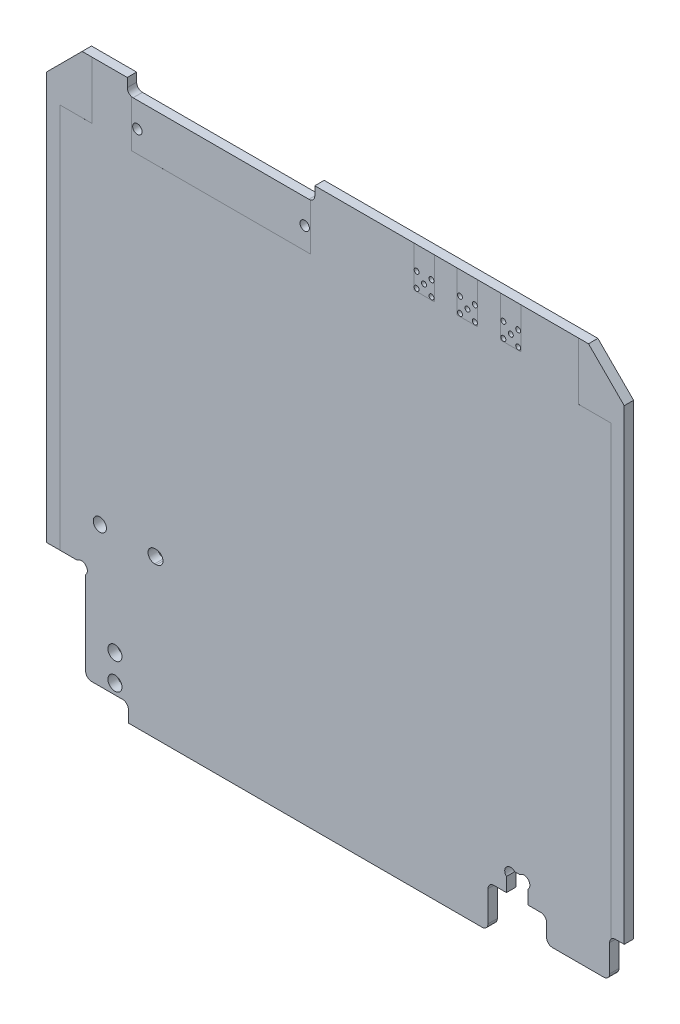
SolidWorks part; units mm, degrees
material "FR4_stuffedProtoboard"
ref_plane "Front Plane" through (0, 0, 0) normal (0, 0, 1) x (1, 0, 0)
ref_plane "Top Plane" through (0, 0, 0) normal (0, 1, 0) x (1, 0, 0)
ref_plane "Right Plane" through (0, 0, 0) normal (1, 0, 0) x (0, 0, -1)
ref_plane "Plane4" through (0, 0, -0.0125) normal (0, 0, -1) x (-1, 0, 0)
sketch "Sketch1" plane through (0, 0, -0.0125) normal (0, 0, -1) x (-1, 0, 0)
  line L0 (35.3, -50) -> (35.3, -48)
  line L1 (36.3, -47) -> (45.8, -47)
  line L2 (46.8, -46) -> (46.8, -41.4)
  line L3 (47.8, -40.4) -> (49.3, -40.4)
  line L4 (49.3, -40.4) -> (49.3, 39.2)
  line L5 (49.3, 39.2) -> (43.2, 45.3)
  line L6 (43.2, 45.3) -> (35.5, 45.3)
  line L7 (35.5, 45.3) -> (35.5, 43.8)
  line L8 (34.5, 42.8) -> (4.5, 42.8)
  line L9 (3.5, 43.8) -> (3.5, 45.3)
  line L10 (3.5, 45.3) -> (-43.2, 45.3)
  line L11 (-43.2, 45.3) -> (-49.3, 39.2)
  line L12 (-49.3, 39.2) -> (-49.3, -40.4)
  line L13 (-49.3, -40.4) -> (-47.8, -40.4)
  line L14 (-46.8, -41.4) -> (-46.8, -46)
  line L15 (-45.8, -47) -> (-36.3, -47)
  line L16 (-35.3, -48) -> (-35.3, -50)
  line L17 (-35.3, -50) -> (35.3, -50)
  line L18 (0, -50) -> (0, 45.3) construction
  line L19 (19.5, 42.8) -> (19.5, 25.5258) construction
  line L20 (-13.87, 41.37) -> (-16.41, 38.83) construction
  line L21 (-21.27, 41.37) -> (-23.81, 38.83) construction
  line L22 (-28.67, 41.37) -> (-31.21, 38.83) construction
  arc A0 (35.3, -48) -> (36.3, -47) centre (36.3, -48) cw
  arc A1 (45.8, -47) -> (46.8, -46) centre (45.8, -46) ccw
  arc A2 (46.8, -41.4) -> (47.8, -40.4) centre (47.8, -41.4) cw
  arc A3 (35.5, 43.8) -> (34.5, 42.8) centre (34.5, 43.8) cw
  arc A4 (4.5, 42.8) -> (3.5, 43.8) centre (4.5, 43.8) cw
  arc A5 (-47.8, -40.4) -> (-46.8, -41.4) centre (-47.8, -41.4) cw
  arc A6 (-46.8, -46) -> (-45.8, -47) centre (-45.8, -46) ccw
  arc A7 (-36.3, -47) -> (-35.3, -48) centre (-36.3, -48) cw
  circle A8 centre (-21.27, 41.37) radius 0.425
  circle A9 centre (-23.81, 41.37) radius 0.425
  circle A10 centre (-22.54, 40.1) radius 0.425
  circle A11 centre (-13.87, 41.37) radius 0.425
  circle A12 centre (-23.81, 38.83) radius 0.425
  circle A13 centre (-16.41, 41.37) radius 0.425
  circle A14 centre (-15.14, 40.1) radius 0.425
  circle A15 centre (-21.27, 38.83) radius 0.425
  circle A16 centre (-28.67, 41.37) radius 0.425
  circle A17 centre (-31.21, 41.37) radius 0.425
  circle A18 centre (-16.41, 38.83) radius 0.425
  circle A19 centre (-29.94, 40.1) radius 0.425
  circle A20 centre (-31.21, 38.83) radius 0.425
  circle A21 centre (-28.67, 38.83) radius 0.425
  circle A22 centre (33.775, 38.54) radius 0.8
  circle A23 centre (5.225, 38.54) radius 0.8
  circle A24 centre (-13.87, 38.83) radius 0.425
  point P35 (-15.14, 40.1)
  dimension "D7" = 2.5
  dimension "D8" = 1.6
  dimension "D9" = 14.275
  dimension "D10" = 4.26
  dimension "D11" = 1
  dimension "D12" = 1
  dimension "D13" = 1
  dimension "D14" = 1
  dimension "D15" = 1
  dimension "D16" = 1
  dimension "D17" = 1
  dimension "D18" = 1
  dimension "D26" = 0.85
  dimension "D1" = 98.6
  dimension "D2" = 95.3
  dimension "D3" = 14
  dimension "D4" = 9.6
  dimension "D5" = 2.5
  dimension "D6" = 3
  dimension "D19" = 14
  dimension "D20" = 2.5
  dimension "D21" = 6.1
  dimension "D22" = 6.1
  dimension "D23" = 32
  dimension "D24" = 2.54
  dimension "D25" = 2.54
  dimension "D28" = 7.4
  dimension "D29" = 3.93
  dimension "D30" = 35.43
  dimension "D31" = 45
  dimension "D32" = 45
  dimension "D33" = 29.8
  dimension "D34" = 50
  dimension "D27" = 3
extrude "Boss-Extrude1" add sketch "Sketch1" against normal blind 1.6
sketch "thermalContacts_lower" plane through (0, 0, -0.0125) normal (0, 0, -1) x (-1, 0, 0)
  line L3 (47, 35.5) -> (47, -41.5)
  line L4 (41.5, 35.5) -> (41.5, 41.5)
  line L5 (41.5, 35.5) -> (47, 35.5)
  line L9 (-47, 35.5) -> (-47, -41.5)
  line L10 (-41.5, 35.5) -> (-47, 35.5)
  line L11 (-41.5, 35.5) -> (-41.5, 41.5)
  line L14 (-41.5, 41.5) -> (-41.5, 47)
  line L15 (-41.5, 41.5) -> (-49.5, 41.5) construction
  line L18 (41.5, 41.5) -> (41.5, 48.7577)
  line L19 (41.5, 41.5) -> (49.5, 41.5) construction
  line L20 (47, -41.5) -> (59.8273, -41.5)
  line L21 (59.8273, -41.5) -> (59.8273, 48.7577)
  line L22 (-56.1922, 47) -> (-41.5, 47)
  line L23 (41.5, 48.7577) -> (59.8273, 48.7577)
  line L24 (-56.1922, 47) -> (-56.1922, -41.5)
  line L25 (-47, -41.5) -> (-56.1922, -41.5)
  line L26 (43.2, 45.3) -> (35.5, 45.3) construction
  line L27 (49.3, -40.4) -> (49.3, 39.2) construction
  line L28 (-35.3, -50) -> (35.3, -50) construction
  line L29 (-49.3, 39.2) -> (-49.3, -40.4) construction
  line L30 (3.5, 45.3) -> (-43.2, 45.3) construction
  dimension "D1" = 9.8
  dimension "D2" = 7.8
  dimension "D3" = 2.3
  dimension "D4" = 8.5
  dimension "D5" = 8.5
  dimension "D6" = 2.3
  dimension "D7" = 7.8
  dimension "D8" = 9.8
sketch "thermalContacts_upper" plane through (0, 0, 1.5875) normal (0, 0, 1) x (1, 0, 0)
  line L3 (-47, 35.5) -> (-47, -41.5)
  line L4 (-41.5, 35.5) -> (-41.5, 41.5)
  line L5 (-41.5, 35.5) -> (-47, 35.5)
  line L9 (47, 35.5) -> (47, -41.5)
  line L10 (41.5, 35.5) -> (47, 35.5)
  line L11 (41.5, 35.5) -> (41.5, 41.5)
  line L14 (41.5, 41.5) -> (41.5, 47)
  line L15 (41.5, 41.5) -> (49.5, 41.5) construction
  line L18 (-41.5, 41.5) -> (-41.5, 47)
  line L19 (-41.5, 41.5) -> (-49.5, 41.5) construction
  line L20 (47, -41.5) -> (59.8273, -41.5)
  line L21 (59.8273, -41.5) -> (59.8273, 47)
  line L22 (59.8273, 47) -> (41.5, 47)
  line L23 (-41.5, 47) -> (-56.1922, 47)
  line L24 (-56.1922, 47) -> (-56.1922, -41.5)
  line L25 (-56.1922, -41.5) -> (-47, -41.5)
extrude "Cut-Extrude1" cut sketch "thermalContacts_lower" against normal blind 0.0001
extrude "Cut-Extrude2" cut sketch "thermalContacts_upper" against normal blind 0.0001
sketch "partFootprints" plane through (0, 0, 1.5875) normal (0, 0, 1) x (1, 0, 0)
  line L0 (-34.74, 34.84) -> (-34.74, 42.8292)
  line L1 (-4.26, 34.84) -> (-34.74, 34.84)
  line L2 (-41.5, 45.3) -> (-35.5, 45.3) construction
  line L3 (-36.1132, 45.3) -> (-39.5054, 45.3) construction
  line L4 (-4.26, 34.84) -> (-4.26, 42.8292)
  line L5 (-49.3, -40.4) -> (-49.3, 39.2) construction
  line L6 (13.39, 45.3) -> (13.39, 38.35)
  line L7 (13.39, 38.35) -> (16.89, 38.35)
  line L8 (16.89, 38.35) -> (16.89, 45.3)
  line L9 (16.89, 45.3) -> (13.39, 45.3)
  line L10 (20.79, 45.3) -> (20.79, 38.35)
  line L11 (20.79, 38.35) -> (24.29, 38.35)
  line L12 (24.29, 38.35) -> (24.29, 45.3)
  line L13 (24.29, 45.3) -> (20.79, 45.3)
  line L14 (28.19, 45.3) -> (28.19, 38.35)
  line L15 (28.19, 38.35) -> (31.69, 38.35)
  line L16 (31.69, 38.35) -> (31.69, 45.3)
  line L17 (31.69, 45.3) -> (28.19, 45.3)
  line L19 (14.12, 38.35) -> (16.16, 38.35) construction
  line L20 (-34.74, 42.8292) -> (-4.26, 42.8292)
  line L21 (-3.5, 45.3) -> (41.5, 45.3) construction
  line L22 (14.12, 38.35) -> (16.16, 38.35) construction
  line L23 (13.39, 41.85) -> (13.39, 38.35) construction
  line L24 (16.89, 41.85) -> (16.89, 38.35) construction
  line L25 (13.39, 41.85) -> (13.39, 38.35) construction
  line L26 (16.89, 41.85) -> (16.89, 38.35) construction
  arc A0 (-35.5, 43.8) -> (-34.5, 42.8) centre (-34.5, 43.8) ccw construction
  arc A1 (-4.5, 42.8) -> (-3.5, 43.8) centre (-4.5, 43.8) ccw construction
  dimension "D1" = 10.46
  dimension "D2" = 14.56
  dimension "D3" = 30.48
  dimension "D7" = 7.4
  dimension "D6" = 3
extrude "Cut-Extrude3" cut sketch "partFootprints" against normal blind 0.0001
sketch "Sketch2" plane through (0, 0, 1.5875) normal (0, 0, 1) x (1, 0, 0)
  line L0 (35.1, -50) -> (35.1, -37.5518) construction
  line L1 (35.3, -50) -> (-35.3, -50) construction
  line L2 (27, -50) -> (27, -36.9095) construction
  line L3 (35.3, -48) -> (35.3, -50) construction
  line L4 (29.2, -42.8) -> (29.2, -40.4142)
  line L5 (27, -39) -> (35.1, -39) construction
  line L6 (30.6142, -39) -> (31.4858, -39)
  line L7 (32.9, -40.4142) -> (32.9, -42.8)
  line L8 (26.05, -50) -> (36.05, -50)
  line L9 (30.6142, -39) -> (31.4858, -39) construction
  line L10 (26.05, -50) -> (26.05, -42.8)
  line L11 (26.05, -42.8) -> (29.2, -42.8)
  line L12 (31.05, -39) -> (31.05, -50) construction
  line L13 (36.05, -42.8) -> (32.9, -42.8)
  line L14 (36.05, -50) -> (36.05, -42.8)
  line L15 (48.0683, 27.2) -> (36.7758, 27.2) construction
  line L16 (48.0683, 35.5) -> (35.6387, 35.5) construction
  line L17 (42.1, 29.55) -> (39.0071, 29.55) construction
  line L18 (38.3, 35.5) -> (38.3, 27.2) construction
  line L19 (38.3, 30.2571) -> (38.3, 32.4429) construction
  line L20 (39.0071, 33.15) -> (42.1, 33.15) construction
  line L21 (49.3, 29.1) -> (49.3, 33.6) construction
  line L22 (38.3, 30.2571) -> (38.3, 32.4429) construction
  line L23 (49.3, 29.1) -> (42.1, 29.1) construction
  line L24 (42.1, 29.1) -> (42.1, 29.55) construction
  line L25 (38.3, 31.35) -> (49.3, 31.35) construction
  line L26 (42.1, 33.6) -> (42.1, 33.15) construction
  line L27 (49.3, 33.6) -> (42.1, 33.6) construction
  line L28 (49.3, -40.4) -> (49.3, 39.2) construction
  line L30 (31.69, 45.3) -> (41.5, 45.3) construction
  arc A0 (29.2, -40.4142) -> (30.6142, -39) centre (29.9071, -39.7071) cw
  arc A1 (31.4858, -39) -> (32.9, -40.4142) centre (32.1929, -39.7071) cw
  arc A2 (39.0071, 29.55) -> (38.3, 30.2571) centre (38.6536, 29.9036) cw construction
  arc A3 (38.3, 32.4429) -> (39.0071, 33.15) centre (38.6536, 32.7964) cw construction
  point P8 (35.3, -49)
  point P39 (38.3, 31.35)
  point P46 (38.3, 31.35)
  point P47 (38.3, 29.55)
  point P48 (38.3, 33.15)
  point P57 (31.05, -39)
  point P59 (32.9, -39)
  point P60 (29.2, -39)
  dimension "D5" = 1
  dimension "D8" = 0.5
  dimension "D1" = 0.2
  dimension "D2" = 8.3
  dimension "D3" = 3.7
  dimension "D4" = 11
  dimension "D6" = 3.8
  dimension "D7" = 10
  dimension "D9" = 3.6
  dimension "D10" = 11
  dimension "D11" = 3.8
  dimension "D12" = 4.5
  dimension "D13" = 9.8
  dimension "D14" = 8.3
extrude "Cut-Extrude4" cut sketch "Sketch2" against normal through all
sketch "Sketch3" plane through (0, 0, 1.5875) normal (0, 0, 1) x (1, 0, 0)
  line L0 (45.8, -47) -> (36.3, -47) construction
  line L1 (31.741, -47) -> (39.5208, -47)
  line L2 (31.741, -47) -> (31.741, -52.1552)
  line L3 (31.741, -52.1552) -> (39.5208, -52.1552)
  line L4 (39.5208, -47) -> (39.5208, -52.1552)
extrude "Cut-Extrude5" cut sketch "Sketch3" against normal blind 10
fillet "Fillet1" radius 1 4 edges at (36.05, -42.8, 0.7875) (26.05, -42.8, 0.7875) (36.05, -47, 0.7875) (26.05, -50, 0.7875)
sketch "Sketch4" plane through (0, 0, 1.5875) normal (0, 0, 1) x (1, 0, 0)
  line L0 (-36.3, -47) -> (-45.8, -47) construction
  line L1 (-51.3808, -30.3) -> (-44.0142, -30.3)
  line L2 (-51.3808, -30.3) -> (-51.3808, -47)
  line L3 (-51.3808, -47) -> (-42.6, -47)
  line L4 (-42.6, -31.7142) -> (-42.6, -47)
  line L5 (-42.8, -37.156) -> (-42.8, -48.7489) construction
  line L6 (-44.0142, -30.3) -> (-42.6, -30.3) construction
  line L7 (-42.6, -30.3) -> (-42.6, -31.7142) construction
  arc A0 (-44.0142, -30.3) -> (-42.6, -31.7142) centre (-43.3071, -31.0071) cw
  point P11 (-42.6, -30.3)
  dimension "D1" = 1
  dimension "D2" = 0.2
  dimension "D3" = 16.7
extrude "Cut-Extrude6" cut sketch "Sketch4" against normal through all
fillet "Fillet2" radius 1 1 edges at (-42.6, -47, 0.7875)
sketch "Sketch5" plane through (0, 0, 1.5875) normal (0, 0, 1) x (1, 0, 0)
  line L1 (-30.525, -24.225) -> (-30.825, -24.225)
  line L3 (-30.825, -21.975) -> (-30.525, -21.975)
  line L4 (-49.3, -30.3) -> (-49.3, 39.2) construction
  line L5 (-36.3, -47) -> (-41.6, -47) construction
  circle A1 centre (-40.175, -23.1) radius 1.125
  arc A4 (-30.825, -21.975) -> (-30.825, -24.225) centre (-30.825, -23.1) ccw
  arc A5 (-30.525, -24.225) -> (-30.525, -21.975) centre (-30.525, -23.1) ccw
  dimension "D1" = 2.25
  dimension "D4" = 1.125
  dimension "D2" = 9.125
  dimension "D3" = 23.9
  dimension "D5" = 0.3
  dimension "D6" = 18.475
extrude "Cut-Extrude7" cut sketch "Sketch5" against normal through all
sketch "Sketch6" plane through (0, 0, 1.5875) normal (0, 0, 1) x (1, 0, 0)
  circle A1 centre (-37.6, -40.75) radius 1.2
  circle A2 centre (-37.6, -45.25) radius 1.2 construction
  circle A3 centre (-37.6, -45.25) radius 1.2
  circle A4 centre (-37.6, -40.75) radius 1.2 construction
extrude "Cut-Extrude8" cut sketch "Sketch6" against normal through all
